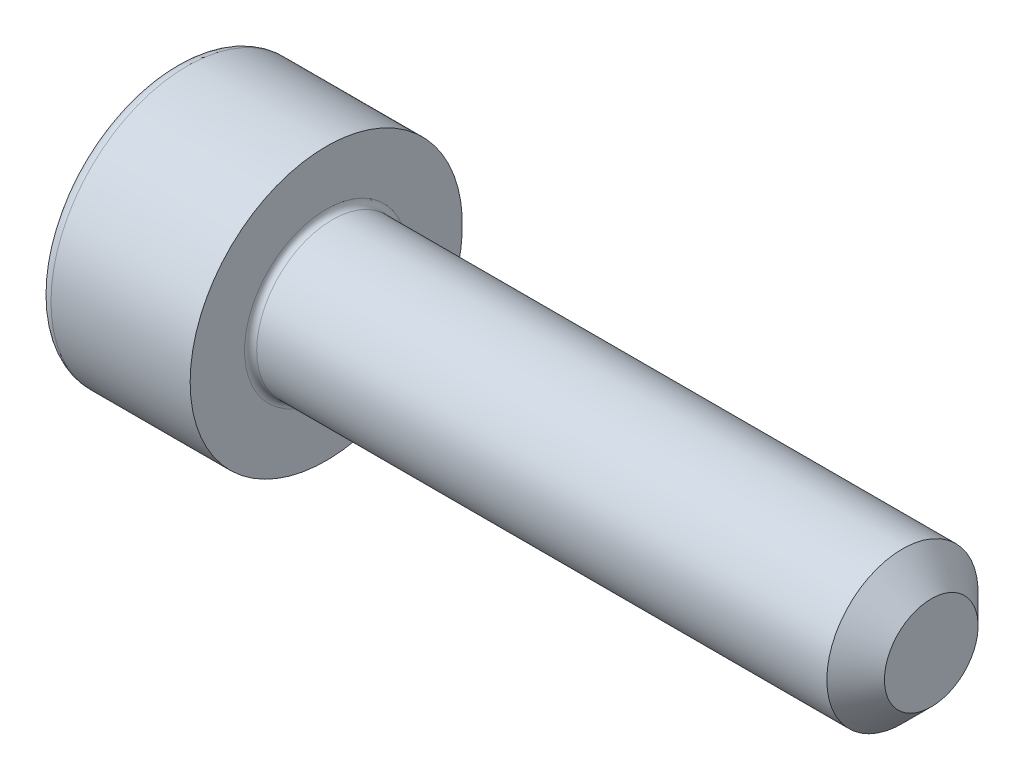
SolidWorks part; units mm, degrees
revolve "Base-Revolve" add sketch "BodySke"
sketch "BodySke" plane through (0, 0, 0) normal (0, 0, 1) x (1, 0, 0)
  line L0 (0, 0) -> (0, 2.25)
  line L1 (0, 2.25) -> (2.5, 2.25)
  line L2 (2.5, 2.25) -> (2.5, 1.25)
  line L3 (2.5, 1.25) -> (12.024, 1.25)
  line L4 (12.5, 0.774) -> (12.5, 0)
  line L5 (12.5, 0) -> (0, 0)
  line L6 (-31.75, 0) -> (127, 0) construction
  line L8 (12.5, 0.774) -> (12.024, 1.25)
  line L10 (12.5, -0.774) -> (12.024, -1.25) construction
  line L11 (2.9, 9.525) -> (2.9, 3.175) construction
  line L12 (4.5, 9.525) -> (4.5, 3.175) construction
  line L13 (-47.5, 9.525) -> (-47.5, 3.175) construction
  dimension "Head_ht" = 2.5
  dimension "Length" = 10
  dimension "Body_ch_ang" = 45
  dimension "Diameter" = 2.5
  dimension "Minor_dia" = 1.548
  dimension "Advance" = 0.4
  dimension "Thread_nom" = 8
  dimension "Thread_length" = 60
  dimension "Head_dia" = 4.5
cosmetic thread "ThreadCosmetic" [suppressed]
fillet "Fillet1" radius 0.1 1 edges at (2.5, 0, 1.25)
fillet "Fillet2" radius 0.2 1 edges at (0, 0, 2.25)
ref_plane "Plane1" through (0, 0, 0) normal (0, 0, 1) x (1, 0, 0)
ref_plane "Plane2" through (0, 0, 0) normal (0, 1, 0) x (1, 0, 0)
ref_plane "Plane3" through (0, 0, 0) normal (1, 0, 0) x (0, 0, -1)
sketch "Sketch2" plane through (0, 0, 0) normal (0, 0, 1) x (1, 0, 0)
  line L0 (0, 0.76) -> (1, 0.76)
  line L1 (1, 0.76) -> (1.4388, 0)
  line L2 (-31.75, 0) -> (127, 0) construction
  line L3 (1.4388, 0) -> (0, 0)
  line L4 (0, 0) -> (0, 0.76)
  line L6 (0, 0) -> (47.625, 0) construction
  dimension "D1" = 0.76
  dimension "D2" = 60
  dimension "Depth" = 1
revolve "Hex-PreBroach" cut sketch "Sketch2" angle 360 about L6
sketch "Sketch3" plane through (0, 0, 0) normal (-1, 0, 0) x (0, 0.5, 0.866)
  line L0 (0.4388, 0.76) -> (-0.4388, 0.76)
  line L1 (-0.4388, 0.76) -> (-0.8776, 0)
  line L2 (0.4388, 0.76) -> (0.8776, 0)
  line L3 (0.4388, -0.76) -> (0.8776, 0)
  line L4 (0.4388, -0.76) -> (-0.4388, -0.76)
  line L5 (-0.4388, -0.76) -> (-0.8776, 0)
  dimension "D1" = 0.76
  dimension "D2" = 0.76
  dimension "Hex_size" = 1.52
extrude "Hex" cut sketch "Sketch3" against normal blind 1
sketch "ThdSchSke" plane through (0, 0, 0) normal (0, 0, 1) x (1, 0, 0)
  line L0 (4.5, -0.774) -> (4.1667, -1.25)
  line L1 (4.5, -0.774) -> (4.8333, -1.25)
  line L2 (4.8333, -1.25) -> (4.8333, -1.5625)
  line L3 (-3.175, 0) -> (5.1513, 0) construction
  line L4 (0, 2.05) -> (0, -2.05) construction
  line L5 (4.8333, -1.5625) -> (4.1667, -1.5625)
  line L6 (4.1667, -1.5625) -> (4.1667, -1.25)
  dimension "Thread_minor" = 1.548
  dimension "Diameter" = 2.5
  dimension "Start" = 4.5
revolve "ThreadSchematic" [suppressed] cut sketch "ThdSchSke" angle 360 about L3
pattern_linear "ThdSchPat" [suppressed]
equation "\"D2@Sketch3\" = \"Hex_size@Sketch3\" / 2"
equation "\"D1@Sketch3\" = \"Hex_size@Sketch3\" / 2"
equation "\"D1@Sketch2\" = \"Hex_size@Sketch3\" / 2"
equation "\"Thread_minor@ThreadCosmetic\"  =  \"Minor_dia@BodySke\""
equation "\"Depth@Sketch2\" =  \"Key_eng@Hex\""
equation "\"Thread_length@ThreadCosmetic\" = ((sgn( (\"Length@BodySke\" - \"Advance@BodySke\" * 3.0) - \"Thread_nom@BodySke\" )-1)*( (\"Length@BodySke\" - \"Advance@BodySke\" * 3.0) - \"Thread_nom@BodySke\" ))/-2+ \"Thread_nom@BodySke\""
equation "\"Thread_minor@ThdSchSke\" = \"Minor_dia@BodySke\""
equation "\"Diameter@ThdSchSke\" = \"Diameter@BodySke\""
equation "\"Overcut@ThdSchSke\" = \"Diameter@BodySke\" * 1.25"
equation "\"Start@ThdSchSke\" = \"Head_ht@BodySke\" + \"Length@BodySke\" - \"Thread_length@ThreadCosmetic\"  '---Non-countersunk---"
equation "\"Num_threads@ThdSchPat\" = int( \"Thread_length@ThreadCosmetic\" / \"Advance@BodySke\" + 0.999 )  + 1"
equation "\"Advance@ThdSchPat\" = \"Thread_length@ThreadCosmetic\" /  (\"Num_threads@ThdSchPat\" - 1) 'relax it"
equation "\"Num_threads@ThdSchPat\" = \"Num_threads@ThdSchPat\" - sgn( \"Num_threads@ThdSchPat\" - 1) '---chamfered tips only---"
